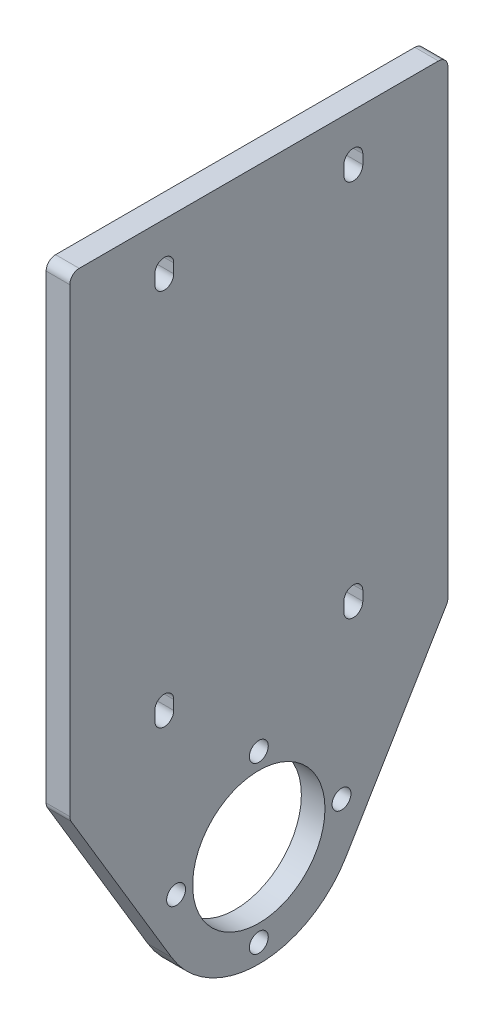
SolidWorks part; units mm, degrees
ref_plane "Front Plane" through (0, 0, 0) normal (0, 0, 1) x (1, 0, 0)
ref_plane "Top Plane" through (0, 0, 0) normal (0, 1, 0) x (1, 0, 0)
ref_plane "Right Plane" through (0, 0, 0) normal (1, 0, 0) x (0, 0, -1)
sketch "Sketch1" plane through (0, 0, 0) normal (1, 0, 0) x (0, 0, -1)
  line L0 (0, 0) -> (0, -75) construction
  line L1 (-40, 50) -> (40, 50)
  line L2 (-40, 50) -> (-40, -50)
  line L3 (-40, -50) -> (40, -50)
  line L4 (40, 50) -> (40, -50)
  line L5 (-40, 50) -> (40, -50) construction
  line L6 (-40, -50) -> (40, 50) construction
  line L7 (0, 0) -> (40, 0) construction
  line L8 (-40, 40) -> (40, 40) construction
  line L9 (-20, 41) -> (-20, 39) construction
  line L10 (-18, 41) -> (-18, 39)
  line L11 (-22, 41) -> (-22, 39)
  line L12 (20, 41) -> (20, 39) construction
  line L13 (18, 41) -> (18, 39)
  line L14 (22, 41) -> (22, 39)
  line L15 (-20, -41) -> (-20, -39) construction
  line L16 (-18, -41) -> (-18, -39)
  line L17 (-22, -41) -> (-22, -39)
  line L18 (20, -41) -> (20, -39) construction
  line L19 (18, -41) -> (18, -39)
  line L20 (22, -41) -> (22, -39)
  line L21 (-40, -50) -> (-18.4526, -86.0341)
  line L22 (40, -50) -> (18.4526, -86.0341)
  arc A0 (-18, 41) -> (-22, 41) centre (-20, 41) ccw
  arc A1 (-22, 39) -> (-18, 39) centre (-20, 39) ccw
  arc A2 (18, 41) -> (22, 41) centre (20, 41) cw
  arc A3 (22, 39) -> (18, 39) centre (20, 39) cw
  arc A4 (-18, -41) -> (-22, -41) centre (-20, -41) cw
  arc A5 (-22, -39) -> (-18, -39) centre (-20, -39) cw
  arc A6 (18, -41) -> (22, -41) centre (20, -41) ccw
  arc A7 (22, -39) -> (18, -39) centre (20, -39) ccw
  circle A8 centre (0, -75) radius 14
  circle A9 centre (0, -75) radius 17.5 construction
  circle A10 centre (17.5, -75) radius 2
  circle A11 centre (0, -92.5) radius 2
  circle A12 centre (-17.5, -75) radius 2
  circle A13 centre (0, -57.5) radius 2
  circle A14 centre (0, -75) radius 21.5
  point P0 (0, 0)
  point P14 (-20, 40)
  point P22 (20, 40)
  point P27 (-20, -40)
  point P34 (20, -40)
  point P51 (0, -75)
  dimension "D2" = 2
  dimension "D6" = 28
  dimension "D7" = 35
  dimension "D8" = 4
  dimension "D10" = 43
  dimension "D11" = 25
  dimension "D1" = 100
  dimension "D3" = 2
  dimension "D4" = 10
  dimension "D5" = 20
  dimension "D12" = 80
  dimension "D9" = 4
extrude "Boss-Extrude1" add sketch "Sketch1" along normal blind 5 contours L4 L1 L2 L3 A7 L20 A6 L19 A1 L11 A0 L10 L14 A3 L13 A2 L17 A5 L16 A4 | A14 L22 L3 L21 | A14 A8 A10 A11 A12 A13
fillet "Fillet1" radius 2 4 edges at (2.5, -50, -40) (2.5, -50, 40) (2.5, 50, -40) (2.5, 50, 40)
